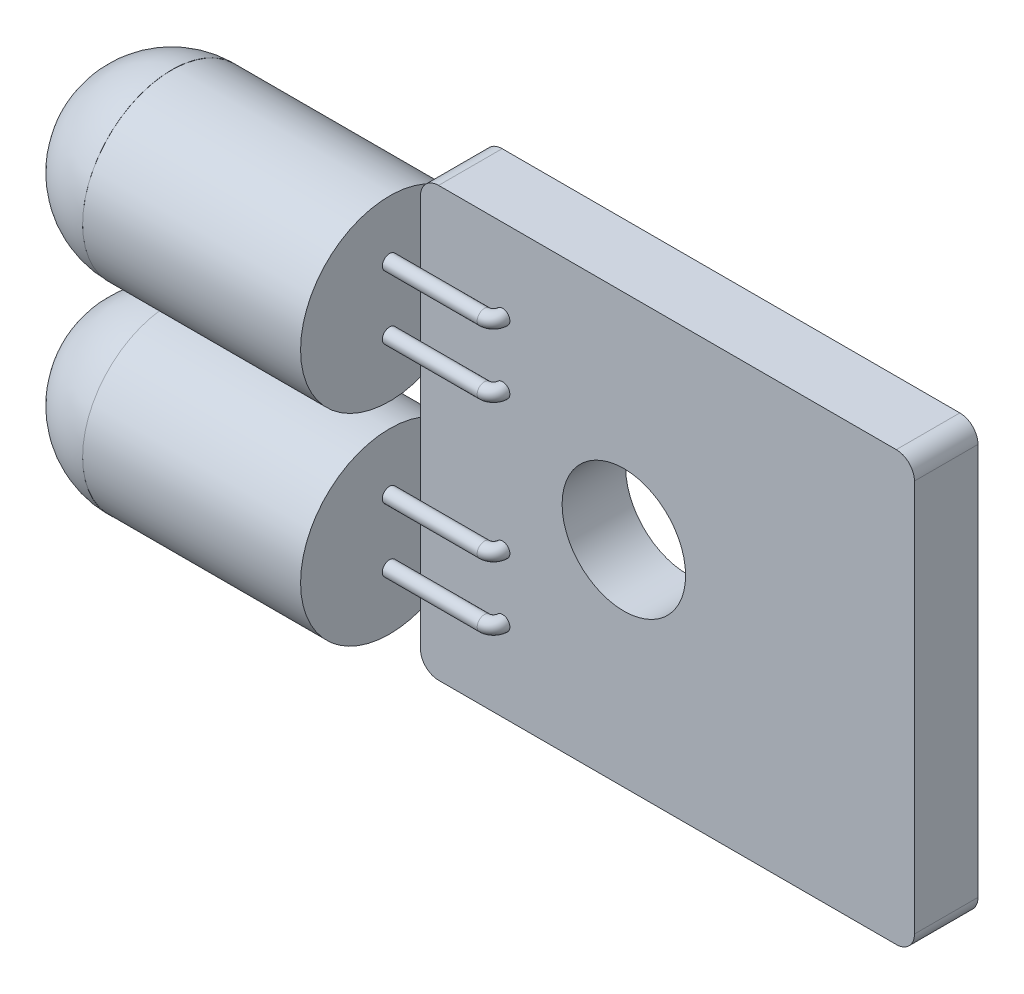
SolidWorks part; units mm, degrees
ref_plane "前视基准面" through (0, 0, 0) normal (0, 0, 1) x (1, 0, 0)
ref_plane "上视基准面" through (0, 0, 0) normal (0, 1, 0) x (1, 0, 0)
ref_plane "右视基准面" through (0, 0, 0) normal (1, 0, 0) x (0, 0, -1)
ref_plane "基准面5" through (-0.6, 0, 0) normal (1, 0, 0) x (0, 0, -1)
sketch "草图1" plane through (0, 0, 0) normal (0, 0, 1) x (1, 0, 0)
  line L1 (0, 0) -> (13.6, 0)
  line L2 (0, 0) -> (0, -11.8)
  line L3 (0, -11.8) -> (13.6, -11.8)
  line L4 (13.6, 0) -> (13.6, -11.8)
  dimension "D1" = 13.6
  dimension "D2" = 11.8
extrude "凸台-拉伸1" add sketch "草图1" along normal blind 1.75
sketch "草图2" plane through (0, 0, 1.75) normal (0, 0, 1) x (1, 0, 0)
  line L0 (-0.6, -2) -> (2.0121, -2)
  line L1 (-0.6, -3.75) -> (-0.6, -4.25)
  line L2 (-0.6, -7.55) -> (-0.6, -8.05)
  line L3 (-2.3025, -5.9) -> (15.3291, -5.9) construction
  line L4 (-0.6, -2.5) -> (2.0121, -2.5)
  line L5 (-0.6, -3.75) -> (2.0121, -3.75)
  line L6 (-0.6, -4.25) -> (2.0121, -4.25)
  line L7 (-0.6, -7.55) -> (2.0121, -7.55)
  line L8 (-0.6, -8.05) -> (2.0121, -8.05)
  line L9 (-0.6, -9.3) -> (2.0121, -9.3)
  line L10 (-0.6, -9.8) -> (2.0121, -9.8)
  line L11 (-0.6, -9.3) -> (-0.6, -9.8)
  line L12 (0, 0) -> (0, -11.8) construction
  line L15 (-0.6, -2) -> (-0.6, -2.5)
  line L16 (2.0121, -2) -> (2.0121, -2.5)
  line L17 (2.0121, -3.75) -> (2.0121, -4.25)
  line L18 (2.0121, -7.55) -> (2.0121, -8.05)
  line L19 (2.0121, -9.3) -> (2.0121, -9.8)
  point P10 (-0.6, -4)
  point P17 (-0.6, -2.25)
  dimension "D1" = 1.9
  dimension "D2" = 3.65
  dimension "D3" = 0.5
  dimension "D4" = 2.0121
extrude "凸台-拉伸2" [suppressed] add sketch "草图2" along normal blind 0.5
sketch "草图3" plane through (-0.6, 0, 0) normal (-1, 0, 0) x (0, 0, 1)
  line L0 (2, -2.5) -> (2, -3.75)
  line L5 (2, -8.05) -> (2, -9.3)
  circle A0 centre (2, -3.125) radius 2.45
  circle A1 centre (2, -8.675) radius 2.45
extrude "凸台-拉伸11" add sketch "草图3" along normal blind 6 contours A0 | A1
ref_plane "基准面2" through (0, -5.9, 1.75) normal (0, -1, 0) x (-1, 0, 0)
ref_plane "基准面6" through (0, -3.12, 1.75) normal (0, -1, 0) x (-1, 0, 0)
sketch "草图5" plane through (0, -3.12, 1.75) normal (0, -1, 0) x (-1, 0, 0)
  line L1 (6.6, -0.25) -> (9.05, -0.25)
  line L2 (6.6, 2.2) -> (6.6, -0.25)
  arc A0 (9.05, -0.25) -> (6.6, 2.2) centre (6.6, -0.25) ccw
revolve "旋转1" add sketch "草图5" angle 360 about L1
sketch "草图6" plane through (0, 0, 0) normal (0, 0, -1) x (-1, 0, 0)
  line L0 (-5.6, 0) -> (-5.6, -11.8)
  line L1 (-13.6, 0) -> (0, 0) construction
  line L2 (0, -11.8) -> (-13.6, -11.8) construction
  circle A0 centre (-5.6, -5.9) radius 1.7
  dimension "D1" = 5.6
extrude "切除-拉伸1" cut sketch "草图6" against normal through all contours L0 A0 | L0 A0
ref_plane "基准面3" through (0, -4, 1.75) normal (0, -1, 0) x (-1, 0, 0)
ref_plane "基准面4" through (0, -2.25, 1.75) normal (0, -1, 0) x (-1, 0, 0)
sketch "草图9" plane through (0, -4, 1.75) normal (0, -1, 0) x (-1, 0, 0)
  line L0 (0.6, -0.25) -> (-2.0121, -0.25)
  arc A0 (-2.2621, 0) -> (-2.0121, -0.25) centre (-2.0121, 0) ccw
sweep "扫描3" add path "草图9" circular profile diameter 0.4 parameters "D3"=0.4
sketch "草图40" plane through (0, -2.25, 1.75) normal (0, -1, 0) x (-1, 0, 0)
  line L0 (0.6, -0.25) -> (-2.0121, -0.25) construction
  line L1 (0.6, -0.25) -> (-2.0121, -0.25)
  arc A0 (-2.2621, 0) -> (-2.0121, -0.25) centre (-2.0121, 0) ccw construction
  arc A1 (-2.2621, 0) -> (-2.0121, -0.25) centre (-2.0121, 0) ccw
sweep "扫描4" add path "草图40" circular profile diameter 0.4 parameters "D3"=0.4
mirror "镜向1" about plane through (0, -5.9, 1.75) normal (0, -1, 0) of "扫描3", "扫描4", "旋转1"
fillet "圆角1" radius 0.5 4 edges at (13.6, 0, 0.875) (0, 0, 0.875) (0, -11.8, 0.875) (13.6, -11.8, 0.875)
